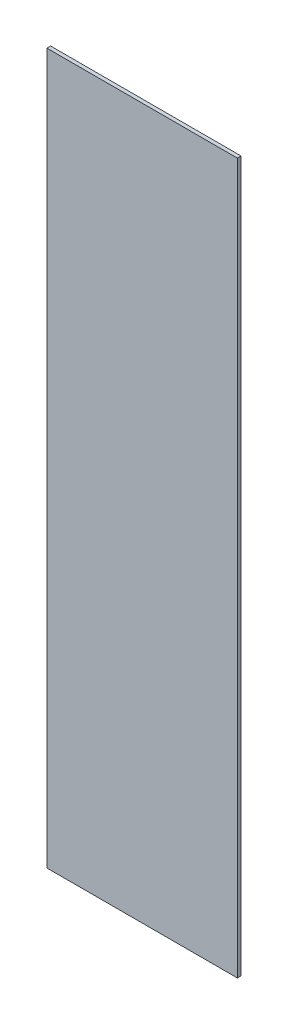
SolidWorks part; units mm, degrees
material "PE High Density"
ref_plane "Front Plane" through (0, 0, 0) normal (0, 0, 1) x (1, 0, 0)
ref_plane "Top Plane" through (0, 0, 0) normal (0, 1, 0) x (1, 0, 0)
ref_plane "Right Plane" through (0, 0, 0) normal (1, 0, 0) x (0, 0, -1)
sketch "Sketch1" plane through (0, 0, 0) normal (0, 0, 1) x (1, 0, 0)
  line L1 (378.5811, -1809.2407) -> (705.6061, -1809.2407)
  line L2 (378.5811, -1809.2407) -> (378.5811, -590.0407)
  line L3 (378.5811, -590.0407) -> (705.6061, -590.0407)
  line L4 (705.6061, -1809.2407) -> (705.6061, -590.0407)
  dimension "D1" = 327.025
  dimension "D2" = 1219.2
extrude "Boss-Extrude1" add sketch "Sketch1" along normal blind 6.35
